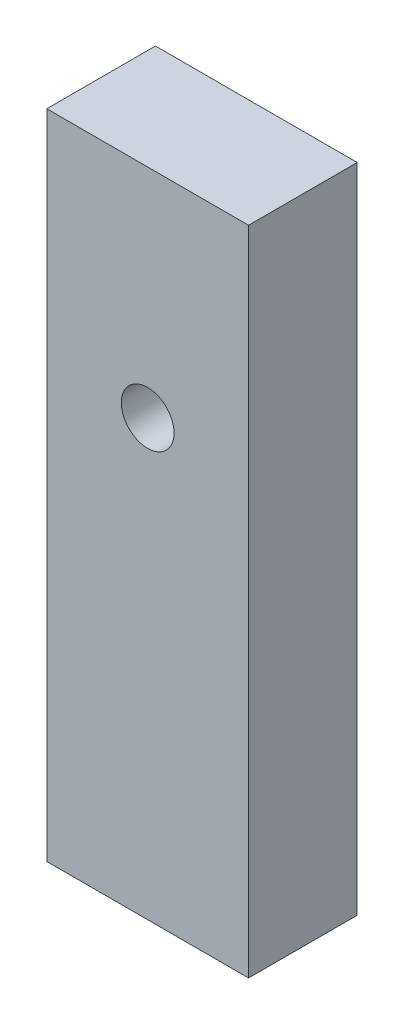
SolidWorks part; units mm, degrees
ref_plane "Front Plane" through (0, 0, 0) normal (0, 0, 1) x (1, 0, 0)
ref_plane "Top Plane" through (0, 0, 0) normal (0, 1, 0) x (1, 0, 0)
ref_plane "Right Plane" through (0, 0, 0) normal (1, 0, 0) x (0, 0, -1)
sketch "Sketch1" plane through (0, 0, 0) normal (0, 0, 1) x (1, 0, 0)
  line L1 (-25.6396, 56.078) -> (-12.6396, 56.078)
  line L2 (-25.6396, 56.078) -> (-25.6396, 14.078)
  line L3 (-25.6396, 14.078) -> (-12.6396, 14.078)
  line L4 (-12.6396, 56.078) -> (-12.6396, 14.078)
  line L5 (-25.6396, 56.078) -> (-12.6396, 14.078) construction
  line L6 (-25.6396, 14.078) -> (-12.6396, 56.078) construction
  point P0 (-19.1396, 35.078)
extrude "Boss-Extrude1" add sketch "Sketch1" along normal blind 7
sketch "Sketch2" plane through (0, 0, 0) normal (0, 0, -1) x (-1, 0, 0)
  line L7 (13.6396, 36.878) -> (24.6396, 36.878)
  line L8 (13.6396, 36.878) -> (13.6396, 33.278)
  line L9 (13.6396, 33.278) -> (24.6396, 33.278)
  line L10 (24.6396, 36.878) -> (24.6396, 33.278)
  line L11 (13.6396, 36.878) -> (24.6396, 33.278) construction
  line L12 (13.6396, 33.278) -> (24.6396, 36.878) construction
  point P12 (19.1396, 35.078)
extrude "Cut-Extrude1" cut sketch "Sketch2" against normal blind 4
sketch "Sketch3" plane through (0, 0, 0) normal (0, 0, 1) x (1, 0, 0)
  circle A0 centre (-19.1396, 42.078) radius 1.7
extrude "Cut-Extrude2" cut sketch "Sketch3" along normal blind 10
